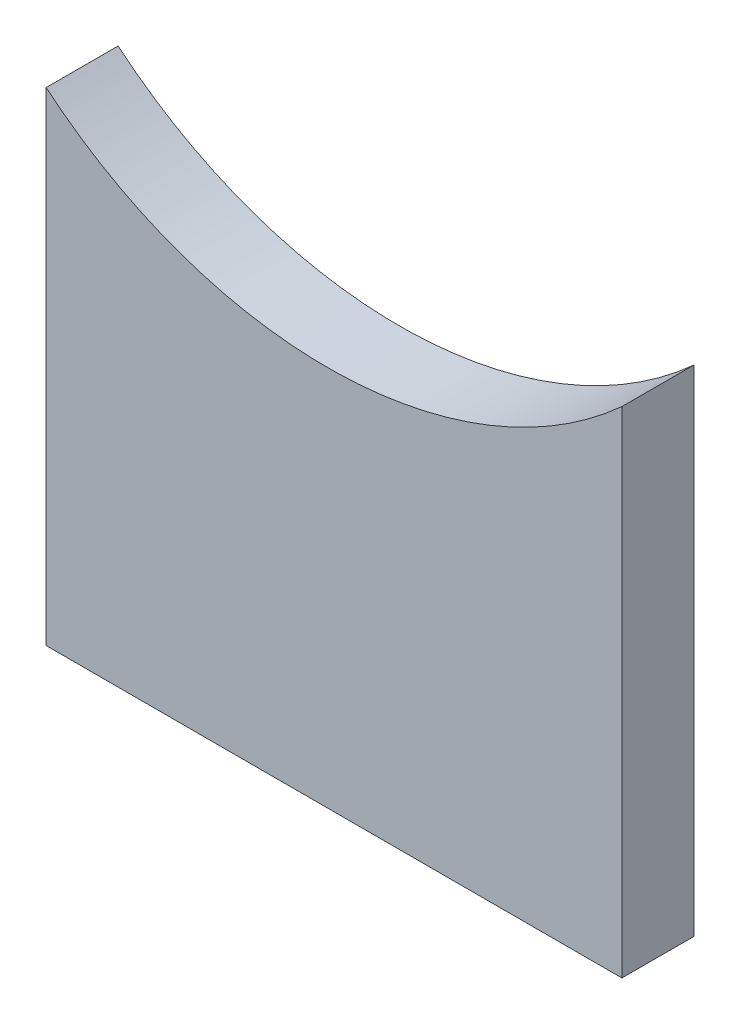
SolidWorks part; units mm, degrees
material "1.7218 (25CrMo4)"
ref_plane "Płaszczyzna XY" through (0, 0, 0) normal (0, 0, 1) x (1, 0, 0)
ref_plane "Płaszczyzna XZ" through (0, 0, 0) normal (0, 1, 0) x (1, 0, 0)
ref_plane "Płaszczyzna YZ" through (0, 0, 0) normal (1, 0, 0) x (0, 0, -1)
sketch "Szkic1" plane through (0, 0, 0) normal (0, 0, 1) x (1, 0, 0)
  line L0 (0, 55.3307) -> (0, 0) construction
  line L1 (0, 0) -> (45.491, 0) construction
  line L2 (0, 31.8557) -> (16, 31.8557)
  line L3 (16, 31.8557) -> (16, 26.1745)
  line L5 (0, 31.8557) -> (0, 0)
  line L6 (16, 0) -> (16, 26.1745)
  line L7 (0, 0) -> (16, 0)
  line L8 (0, 31.8557) -> (0, 0)
  line L9 (16, 0) -> (16, 26.1745)
  line L10 (0, 0) -> (16, 0)
  spline S1 degree 3 poles (16, 26.1745) (9.1813, 23.4108) (2.9905, 26.3813) (0, 31.8557) knots 0.071166 0.071166 0.071166 0.071166 0.277144 0.277144 0.277144 0.277144 weights 0.505895 0.476075 0.559394 0.755852
  dimension "D1" = 0
extrude "Dodanie-wyciągnięcie1" add sketch "Szkic1" along normal blind 2
sketch "Szkic2" plane through (0, 0, 2) normal (0, 0, 1) x (1, 0, 0)
  line L0 (0, 5) -> (16, 5)
  line L4 (16, 0) -> (16, 31.8557)
  line L5 (0, 31.8557) -> (0, 0)
  line L6 (0, 0) -> (16, 0)
  line L7 (16, 0) -> (16, 31.8557)
  line L8 (0, 31.8557) -> (0, 0)
  line L9 (0, 0) -> (16, 0)
  line L11 (16, 31.8557) -> (0, 31.8557)
  line L12 (16, 31.8557) -> (0, 31.8557)
  line M18 (16, 0) -> (16, 31.8557)
  line M20 (0, 31.8557) -> (0, 0)
  line M21 (0, 0) -> (16, 0)
  dimension "D2" = 5
  dimension "D1" = 0
extrude "Wytnij-wyciągnięcie1" cut sketch "Szkic2" against normal blind 5 contours L0 M20 M21 M18
sketch "Szkic6" plane through (0, 0, 0) normal (0, 0, -1) x (-1, 0, 0)
  line L0 (0, 31.8557) -> (-16, 31.8557)
  line L1 (-16, 31.8557) -> (-16, 18.7509)
  line L2 (-16, 5) -> (-16, 31.8557) construction
  line L3 (0, 31.8557) -> (0, 18.4279)
  line L4 (0, 31.8557) -> (0, 5) construction
  arc A1 (0, 18.4279) -> (-16, 18.7509) centre (-7.8139, 27.8085) cw
  dimension "D1" = 12.2087
  dimension "D2" = 7.8139
extrude "Wytnij-wyciągnięcie2" cut sketch "Szkic6" against normal blind 10
